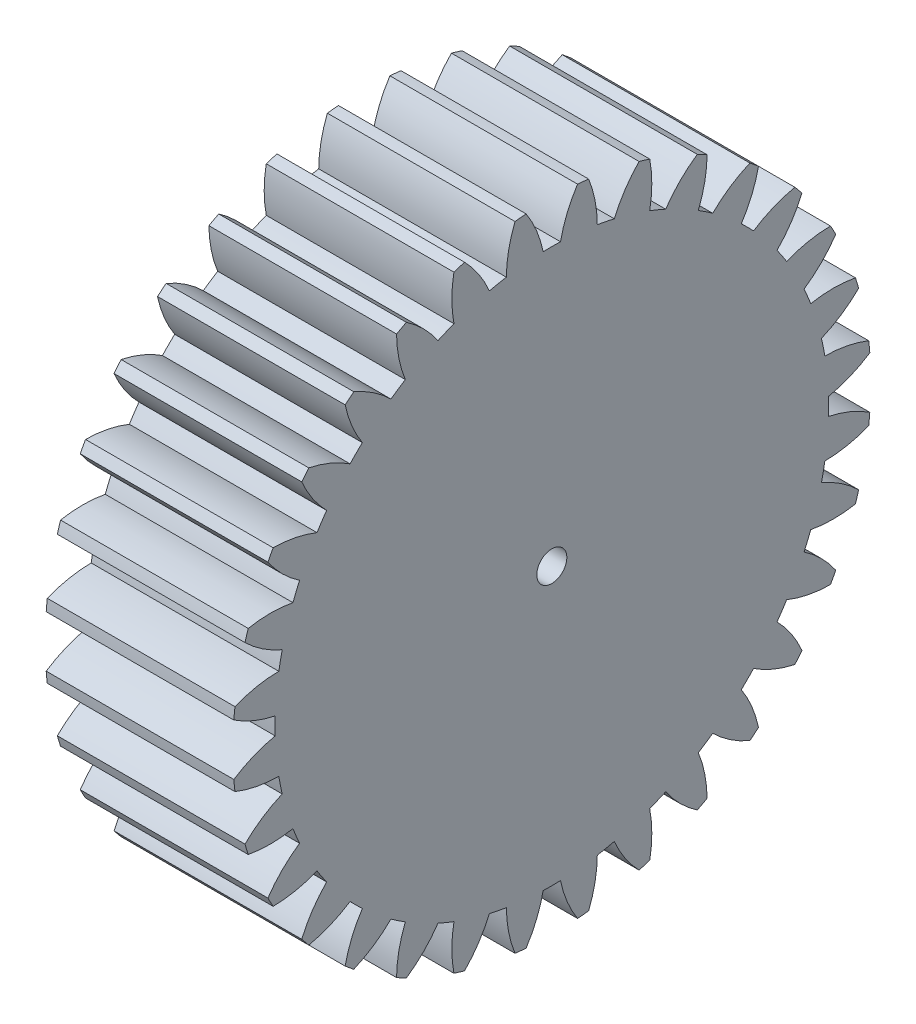
SolidWorks part; units mm, degrees
ref_plane "Plane1" through (0, 0, 0) normal (0, 0, 1) x (1, 0, 0)
ref_plane "Plane2" through (0, 0, 0) normal (0, 1, 0) x (1, 0, 0)
ref_plane "Plane3" through (0, 0, 0) normal (1, 0, 0) x (0, 0, -1)
sketch "HoldingSke" plane through (0, 0, 0) normal (0, 1, 0) x (1, 0, 0)
  line L0 (0, 0) -> (1.6961, -1.0598)
  line L1 (-15, 0) -> (100, 0) construction
  line L2 (0, 0) -> (-2.1039, 2.3779)
  line L3 (0, 0) -> (-11.863, 4.5341)
  line L4 (0, 0) -> (7.3237, 4.5764)
  line L5 (0, 0) -> (-46.8476, -17.4728)
  line L6 (0, 0) -> (-4.1448, -2.7965)
  line L7 (-2.1039, 2.3779) -> (8.6586, 51.2059)
  line L8 (-76.2, 54.61) -> (-76.1, 54.61)
  line L9 (-71.009, 38.7566) -> (-53.1078, 45.2721)
  line L10 (-76.2, 71.12) -> (104.1128, 71.12)
  line L11 (0, 0) -> (-5, 0)
  line L12 (-76.2, 101.6) -> (-76.181, 101.6)
  line L13 (24.9733, 27.94) -> (52.9518, 28.4284)
  line L14 (24.9733, 27.94) -> (24.9743, 27.94)
  line L15 (24.9733, 27.94) -> (100.4006, 29.5858)
  line L16 (-63.627, -0.5) -> (-12.827, -0.5)
  circle A0 centre (0, 0) radius 0.4
  circle A1 centre (0, 0) radius 7.374
  circle A2 centre (0, 0) radius 37.5
  circle A3 centre (0, 0) radius 0.4
  dimension "MHD" = 14.748
  dimension "Hub_dia" = 75
  dimension "Bore" = 0.8
  dimension "MBD" = 0.8
  dimension "Num_teeth" = 32
  dimension "Pitch" = 2
  dimension "Overall_len" = 50
  dimension "Show_teeth" = 32
  dimension "Thickness" = 5
  dimension "OAL" = 50.0001
  dimension "T_dim" = 0.1
  dimension "Ap" = 20
  dimension "H" = 19.05
  dimension "Pitch_radius" = 180.3128
  dimension "Width" = 5
  dimension "Backlash" = 0.019
  dimension "Addendum_fac" = 1
  dimension "Dedendum_fac" = 1.25
  dimension "Clearance_fac" = 0.25
  dimension "Dedendum_add" = 0.001
  dimension "Module" = 0.5
sketch "BasProSke" plane through (0, 0, 0) normal (0, 1, 0) x (1, 0, 0)
  line L0 (-10, 0) -> (60, 0) construction
  line L1 (0, 0) -> (0, 8.5)
  line L2 (0, 0) -> (5, 0)
  line L3 (5, 0) -> (5, 8.5)
  line L4 (5, 8.5) -> (0, 8.5)
  dimension "Thickness" = 5
  dimension "Diameter" = 17
revolve "Base-Revolve" add sketch "BasProSke" angle 360 about L0
sketch "TooCutSke" plane through (0, 0, 0) normal (1, 0, 0) x (0, 0, -1)
  line L1 (0, 0) -> (0, 107) construction
  line L2 (0, 0) -> (-0.4258, 7.9887) construction
  line L3 (0, 0) -> (-1.5667, 15.9069) construction
  line L4 (-0.4258, 7.9887) -> (-0.7833, 7.9534) construction
  arc A0 (0.2309, 7.3704) -> (-0.2309, 7.3704) centre (0, 0) ccw
  arc A1 (0.7014, 8.4965) -> (-0.7014, 8.4965) centre (0, 0) ccw
  circle A2 centre (0, 0) radius 8 construction
  circle A3 centre (0, 0) radius 7.5175 construction
  arc A4 (-0.2309, 7.3704) -> (-0.7014, 8.4965) centre (-3.3647, 6.7225) ccw
  arc A5 (0.7014, 8.4965) -> (0.2309, 7.3704) centre (3.3647, 6.7225) ccw
  dimension "Root_dia" = 14.748
  dimension "Overcut_dia" = 17.0508
  dimension "Pitch_dia" = 16
  dimension "Base_dia" = 15.0351
  dimension "Flank_rad" = 3.2
  dimension "Half_ang" = 5.625
  dimension "Half_CT" = 0.3593
extrude "ToothCut" cut sketch "TooCutSke" along normal through all
fillet "Breaks" [suppressed] radius 0.01
fillet "RootFillets" [suppressed] radius 0.126
pattern_circular "TeethCuts" count 32 every 11.25 about axis through (-10, 0, 0) along (1, 0, 0) of "ToothCut", "RootFillets", "Breaks"
sketch "HubNeaOneSke" plane through (0, 0, 0) normal (-1, 0, 0) x (0, 0, 1)
  circle A0 centre (0, 0) radius 7.374
  dimension "Diameter" = 14.748
extrude "HubNearOne" [suppressed] add sketch "HubNeaOneSke" along normal blind 45.0001
sketch "HubNeaBotSke" plane through (0, 0, 0) normal (-1, 0, 0) x (0, 0, 1)
  circle A0 centre (0, 0) radius 7.374
  dimension "Diameter" = 14.748
extrude "HubNearBoth" [suppressed] add sketch "HubNeaBotSke" along normal blind 22.5
ref_plane "FarPln" through (5, 0, 0) normal (1, 0, 0) x (0, 0, -1)
sketch "HubFarSke" plane through (5, 0, 0) normal (1, 0, 0) x (0, 0, -1)
  circle A0 centre (0, 0) radius 7.374
  dimension "Diameter" = 14.748
extrude "HubFar" [suppressed] add sketch "HubFarSke" along normal blind 22.5
sketch "BorSke" plane through (0, 0, 0) normal (1, 0, 0) x (0, 0, -1)
  circle A0 centre (0, 0) radius 0.4
  dimension "Diameter" = 0.8
extrude "Bore" cut sketch "BorSke" along normal mid plane 100.0001
sketch "KeySke" plane through (0, 0, 0) normal (1, 0, 0) x (0, 0, -1)
  line L0 (-0.05, 0) -> (-0.05, 0.5)
  line L1 (-0.05, 0.5) -> (0.05, 0.5)
  line L2 (0.05, 0.5) -> (0.05, 0)
  line L3 (0, 0) -> (0, 34) construction
  line L4 (-0.05, 0) -> (0.05, 0)
  dimension "Offset" = 0.5
  dimension "Width" = 0.1
extrude "Keyway" [suppressed] cut sketch "KeySke" along normal mid plane 100.0001
pattern_circular "Keyway2" [suppressed] count 2 every 90 about axis through (-10, 0, 0) along (1, 0, 0)
equation "' \"Module@HoldingSke\" = 6.35"
equation "' \"Num_teeth@HoldingSke\" = 12"
equation "' \"Ap@HoldingSke\" =  20"
equation "' \"Ap@HoldingSke\" = 20"
equation "' \"Width@HoldingSke\" = 0.5 * 25.4"
equation "' \"Hub_dia@HoldingSke\"= 1 * 25.4"
equation "' \"Hub_dia@HoldingSke\" = 1 * 25.4"
equation "' \"Overall_len@HoldingSke\" = 1.0 * 25.4"
equation "' \"Bore@HoldingSke\" = 0.75 * 25.4"
equation "' \"T_dim@HoldingSke\" = 0.1 * 25.4"
equation "' \"Width@KeySke\" = 0.25 * 25.4"
equation "' \"Show_teeth@HoldingSke\" = 13"
equation "' \"Backlash@HoldingSke\" = 0.009 * 25.4"
equation "' \"Addendum_fac@HoldingSke\" = 1.0"
equation "' \"Dedendum_fac@HoldingSke\" = 1.25"
equation "' \"Dedendum_add@HoldingSke\" = 0.00005 * 25.4"
equation "' \"Clearance_fac@HoldingSke\" = 0.25"
equation "\"Pitch@HoldingSke\" = 1 / \"Module@HoldingSke\""
equation "\"Overcut_dia@TooCutSke\" = (\"Num_teeth@HoldingSke\" + 2 * \"Addendum_fac@HoldingSke\") / \"Pitch@HoldingSke\" + 0.002 * 25.4"
equation "\"Pitch_dia@TooCutSke\" = \"Num_teeth@HoldingSke\" / \"Pitch@HoldingSke\""
equation "\"Base_dia@TooCutSke\" = \"Num_teeth@HoldingSke\" / \"Pitch@HoldingSke\" * cos((\"Ap@HoldingSke\"  * 3.14159265 / 180))"
equation "\"Root_dia@TooCutSke\" = (\"Num_teeth@HoldingSke\" + 2) / \"Pitch@HoldingSke\" - 2 * (\"Addendum_fac@HoldingSke\" + \"Dedendum_fac@HoldingSke\") / \"Pitch@HoldingSke\" - \"Dedendum_add@HoldingSke\" * 2"
equation "\"Half_ang@TooCutSke\" = 180 / \"Num_teeth@HoldingSke\""
equation "\"Half_CT@TooCutSke\" = \"Num_teeth@HoldingSke\" / \"Pitch@HoldingSke\" * sin((3.14159265 / 2 / \"Num_teeth@HoldingSke\")) / 2 - 7 * \"Backlash@HoldingSke\" / 4"
equation "\"Flank_rad@TooCutSke\" = \"Num_teeth@HoldingSke\" / \"Pitch@HoldingSke\" / 5"
equation "\"Radius@RootFillets\" = \"Clearance_fac@HoldingSke\" / \"Pitch@HoldingSke\" + \"Dedendum_add@HoldingSke\""
equation "\"Break_rad@Breaks\" = 0.02 / \"Pitch@HoldingSke\""
equation "\"Thickness@HoldingSke\" = \"Width@HoldingSke\""
equation "\"OAL@HoldingSke\" = \"Thickness@HoldingSke\""
equation "\"MHD@HoldingSke\" = (\"Num_teeth@HoldingSke\" + 2) / \"Pitch@HoldingSke\" - 2 * (\"Addendum_fac@HoldingSke\" + \"Dedendum_fac@HoldingSke\")  / \"Pitch@HoldingSke\" - \"Dedendum_add@HoldingSke\" * 2"
equation "\"MBD@HoldingSke\" = (\"Num_teeth@HoldingSke\" + 2) / \"Pitch@HoldingSke\" - 2 * (\"Addendum_fac@HoldingSke\" + \"Dedendum_fac@HoldingSke\")  / \"Pitch@HoldingSke\" - \"Dedendum_add@HoldingSke\" * 2 - 0.002 * 25.4"
equation "\"MHD@HoldingSke\" = ((sgn( \"MHD@HoldingSke\" - \"Hub_dia@HoldingSke\" )-1)*( \"MHD@HoldingSke\" - \"Hub_dia@HoldingSke\" ))/-2+ \"Hub_dia@HoldingSke\""
equation "\"MBD@HoldingSke\" = ((sgn( \"MBD@HoldingSke\" - \"Bore@HoldingSke\" )-1)*( \"MBD@HoldingSke\" - \"Bore@HoldingSke\" ))/-2+ \"Bore@HoldingSke\""
equation "\"OAL@HoldingSke\" = ((sgn( \"OAL@HoldingSke\" - \"Overall_len@HoldingSke\" )+1)*( \"OAL@HoldingSke\" - \"Overall_len@HoldingSke\" ))/2 + \"Overall_len@HoldingSke\" + 0.000002 * 25.4"
equation "\"Num_teeth@TeethCuts\" = int( \"Show_teeth@HoldingSke\" ) + 1"
equation "\"Num_teeth@TeethCuts\" = ((sgn( \"Num_teeth@TeethCuts\" - \"Num_teeth@HoldingSke\" )-1)*( \"Num_teeth@TeethCuts\" - \"Num_teeth@HoldingSke\" ))/-2+ \"Num_teeth@HoldingSke\""
equation "\"Num_teeth@TeethCuts\" = ((sgn( \"Num_teeth@TeethCuts\" - 2.0)+1)*( \"Num_teeth@TeethCuts\" - 2.0))/2 +2.0"
equation "\"Angle@TeethCuts\" = 360.0 / \"Num_teeth@HoldingSke\""
equation "\"Diameter@BasProSke\" = (\"Num_teeth@HoldingSke\" + 2 * \"Addendum_fac@HoldingSke\") / \"Pitch@HoldingSke\""
equation "\"Thickness@BasProSke\"  = \"Thickness@HoldingSke\""
equation "' \"Fillet_rad@BasProSke\" =  \"Thickness@HoldingSke\" * 0.05"
equation "' \"Fillet_rad@BasProSke\" = \"Thickness@HoldingSke\" * 0.05"
equation "\"MHD@HoldingSke\" = ((sgn( \"MHD@HoldingSke\" - \"Root_dia@TooCutSke\" )-1)*( \"MHD@HoldingSke\" - \"Root_dia@TooCutSke\" ))/-2+ \"Root_dia@TooCutSke\""
equation "\"Diameter@HubNeaOneSke\" = \"MHD@HoldingSke\""
equation "\"Length@HubNearOne\" = \"OAL@HoldingSke\" - \"Thickness@BasProSke\""
equation "\"Diameter@HubNeaBotSke\" = \"MHD@HoldingSke\""
equation "\"Length@HubNearBoth\" = ( \"OAL@HoldingSke\" - \"Thickness@BasProSke\" ) / 2.0"
equation "\"Thickness@FarPln\" = \"Thickness@BasProSke\""
equation "\"Diameter@HubFarSke\" = \"MHD@HoldingSke\""
equation "\"Length@HubFar\" = ( \"OAL@HoldingSke\" - \"Thickness@BasProSke\" ) / 2.0"
equation "\"Diameter@BorSke\" = \"MBD@HoldingSke\""
equation "\"D1@Bore\" = \"OAL@HoldingSke\" * 2.0"
equation "\"D1@Keyway\" = \"OAL@HoldingSke\" * 2.0"
equation "\"Offset@KeySke\" = \"T_dim@HoldingSke\" + \"MBD@HoldingSke\" / 2.0"
